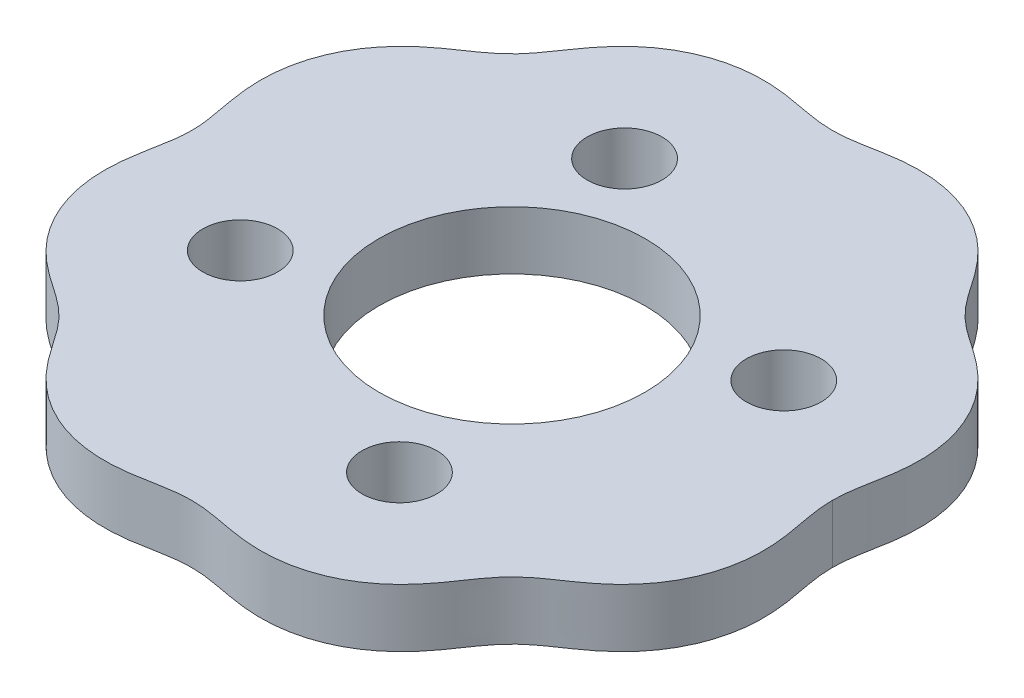
SolidWorks part; units mm, degrees
material "PET"
ref_plane "Front Plane" through (0, 0, 0) normal (0, 0, 1) x (1, 0, 0)
ref_plane "Top Plane" through (0, 0, 0) normal (0, 1, 0) x (1, 0, 0)
ref_plane "Right Plane" through (0, 0, 0) normal (1, 0, 0) x (0, 0, -1)
sketch "Sketch2" plane through (0, 0, 0) normal (0, 1, 0) x (1, 0, 0)
  line L0 (-38.5, 0) -> (38.5, 0) construction
  spline S0 degree 4 poles (38.1584, 16.3054) (38.2988, 15.991) (38.5624, 15.3567) (38.9037, 14.3799) (39.2498, 13.0497) (39.4657, 11.7929) (39.5812, 10.6379) (39.6179, 9.5697) (39.6051, 8.63) (39.5377, 7.649) (39.4431, 6.7539) (39.2854, 5.7098) (39.1515, 4.943) (38.9539, 3.8904) (38.8677, 3.4303) (38.801, 3.0463) (38.7527, 2.7604) (38.7172, 2.5417) (38.6781, 2.2874) (38.6248, 1.9059) (38.5598, 1.3568) (38.5067, 0.6636) (38.4908, -0.1341) (38.5223, -0.93) (38.5973, -1.7236) (38.714, -2.5565) (38.8656, -3.429) (39.0392, -4.3425) (39.2166, -5.3006) (39.3735, -6.2623) (39.4981, -7.2289) (39.6027, -8.4428) (39.6384, -10.0805) (39.4713, -12.1349) (38.9177, -14.5567) (37.9169, -17.0213) (36.6319, -19.1322) (35.1813, -20.8902) (33.6686, -22.3296) (32.1775, -23.5049) (30.6768, -24.5364) (29.2303, -25.5119) (27.9082, -26.5342) (26.7634, -27.6481) (25.705, -28.9579) (24.7073, -30.419) (23.6657, -31.9562) (22.4771, -33.4984) (21.0293, -35.0529) (19.267, -36.5367) (17.158, -37.8472) (14.7024, -38.8713) (11.8141, -39.559) (9.0199, -39.7053) (6.4233, -39.4363) (4.1359, -38.9993) (2.4195, -38.6732) (0.7782, -38.4852) (-0.7782, -38.4854) (-2.4196, -38.6729) (-4.1357, -38.9997) (-5.947, -39.3446) (-7.8752, -39.5874) (-9.9954, -39.6537) (-12.2881, -39.4466) (-15.349, -38.7168) (-18.2043, -37.3449) (-20.5778, -35.5386) (-22.4768, -33.4983) (-23.6659, -31.9563) (-24.7071, -30.4189) (-25.7051, -28.9579) (-26.7634, -27.6481) (-27.9082, -26.5342) (-29.2303, -25.5119) (-30.6768, -24.5364) (-32.1775, -23.5049) (-33.6686, -22.3296) (-35.1813, -20.8902) (-36.6319, -19.1322) (-37.9169, -17.0213) (-38.9177, -14.5567) (-39.4713, -12.1349) (-39.6384, -10.0805) (-39.6027, -8.4428) (-39.4981, -7.2289) (-39.3891, -6.3832) (-39.2754, -5.6612) (-39.1709, -5.0613) (-39.0832, -4.5821) (-38.9934, -4.1033) (-38.9038, -3.6244) (-38.803, -3.069) (-38.6971, -2.4358) (-38.5973, -1.7236) (-38.5223, -0.93) (-38.4908, -0.1341) (-38.5067, 0.6636) (-38.5598, 1.3568) (-38.6248, 1.9059) (-38.6781, 2.2874) (-38.7172, 2.5417) (-38.7527, 2.7604) (-38.801, 3.0463) (-38.8677, 3.4303) (-38.9539, 3.8904) (-39.1515, 4.943) (-39.2854, 5.7098) (-39.4431, 6.7539) (-39.5377, 7.649) (-39.6051, 8.63) (-39.6179, 9.5697) (-39.5812, 10.6379) (-39.4657, 11.7929) (-39.2498, 13.0497) (-38.9037, 14.3799) (-38.5624, 15.3567) (-38.2988, 15.991) (-38.1584, 16.3054) knots 0 0 0 0 0 0.00848 0.016961 0.025441 0.033921 0.039806 0.045692 0.051577 0.057462 0.063348 0.069233 0.075119 0.081004 0.083459 0.084687 0.085914 0.087142 0.08837 0.090825 0.095736 0.100646 0.105557 0.110467 0.115378 0.120289 0.126296 0.132303 0.13831 0.144317 0.150324 0.156331 0.168345 0.184674 0.201003 0.217332 0.233662 0.245354 0.257046 0.268738 0.28043 0.290252 0.300073 0.309894 0.319715 0.331705 0.343696 0.355686 0.367676 0.384005 0.400334 0.416664 0.432993 0.456925 0.468892 0.480858 0.490429 0.5 0.509571 0.519142 0.531108 0.543075 0.555041 0.567007 0.583336 0.599666 0.632324 0.644314 0.656304 0.668295 0.680285 0.690106 0.699927 0.709748 0.71957 0.731262 0.742954 0.754646 0.766338 0.782668 0.798997 0.815326 0.831655 0.843669 0.849676 0.855683 0.86169 0.864694 0.867697 0.870701 0.873704 0.876708 0.879711 0.884622 0.889533 0.894443 0.899354 0.904264 0.909175 0.91163 0.912858 0.914086 0.915313 0.916541 0.918996 0.924881 0.930767 0.936652 0.942538 0.948423 0.954308 0.960194 0.966079 0.974559 0.983039 0.99152 1 1 1 1 1 construction
  spline S1 degree 4 poles (38.5, 0) (38.5, -0.133) (38.5043, -0.4652) (38.5285, -0.9959) (38.5973, -1.7236) (38.714, -2.5565) (38.8656, -3.429) (39.0392, -4.3425) (39.2166, -5.3006) (39.3735, -6.2623) (39.4981, -7.2289) (39.6027, -8.4428) (39.6384, -10.0805) (39.4713, -12.1349) (38.9177, -14.5567) (37.9169, -17.0213) (36.6319, -19.1322) (35.1813, -20.8902) (33.6686, -22.3296) (32.1775, -23.5049) (30.6768, -24.5364) (29.2303, -25.5119) (27.9082, -26.5342) (26.7634, -27.6481) (25.705, -28.9579) (24.7073, -30.419) (23.6657, -31.9562) (22.4771, -33.4984) (21.0293, -35.0529) (19.267, -36.5367) (17.158, -37.8472) (14.7024, -38.8713) (11.8141, -39.559) (9.0199, -39.7053) (6.4233, -39.4363) (4.1359, -38.9993) (2.4195, -38.6732) (0.7782, -38.4852) (-0.7782, -38.4854) (-2.4196, -38.6729) (-4.1357, -38.9997) (-5.947, -39.3446) (-7.8752, -39.5874) (-9.9954, -39.6537) (-12.2881, -39.4466) (-15.349, -38.7168) (-18.2043, -37.3449) (-20.5778, -35.5386) (-22.4768, -33.4983) (-23.6659, -31.9563) (-24.7071, -30.4189) (-25.7051, -28.9579) (-26.7634, -27.6481) (-27.9082, -26.5342) (-29.2303, -25.5119) (-30.6768, -24.5364) (-32.1775, -23.5049) (-33.6686, -22.3296) (-35.1813, -20.8902) (-36.6319, -19.1322) (-37.9169, -17.0213) (-38.9177, -14.5567) (-39.4713, -12.1349) (-39.6384, -10.0805) (-39.6027, -8.4428) (-39.4981, -7.2289) (-39.3891, -6.3832) (-39.2754, -5.6612) (-39.1709, -5.0613) (-39.0832, -4.5821) (-38.9934, -4.1033) (-38.9038, -3.6244) (-38.803, -3.069) (-38.6971, -2.4358) (-38.5973, -1.7236) (-38.5285, -0.9959) (-38.5043, -0.4652) (-38.5, -0.133) (-38.5, 0) knots 0.102277 0.102277 0.102277 0.102277 0.102277 0.105557 0.110467 0.115378 0.120289 0.126296 0.132303 0.13831 0.144317 0.150324 0.156331 0.168345 0.184674 0.201003 0.217332 0.233662 0.245354 0.257046 0.268738 0.28043 0.290252 0.300073 0.309894 0.319715 0.331705 0.343696 0.355686 0.367676 0.384005 0.400334 0.416664 0.432993 0.456925 0.468892 0.480858 0.490429 0.5 0.509571 0.519142 0.531108 0.543075 0.555041 0.567007 0.583336 0.599666 0.632324 0.644314 0.656304 0.668295 0.680285 0.690106 0.699927 0.709748 0.71957 0.731262 0.742954 0.754646 0.766338 0.782668 0.798997 0.815326 0.831655 0.843669 0.849676 0.855683 0.86169 0.864694 0.867697 0.870701 0.873704 0.876708 0.879711 0.884622 0.889533 0.894443 0.897723 0.897723 0.897723 0.897723 0.897723
  spline S2 degree 4 poles (38.5, 0) (38.5, 0.133) (38.5043, 0.4652) (38.5285, 0.9959) (38.5973, 1.7236) (38.714, 2.5565) (38.8656, 3.429) (39.0392, 4.3425) (39.2166, 5.3006) (39.3735, 6.2623) (39.4981, 7.2289) (39.6027, 8.4428) (39.6384, 10.0805) (39.4713, 12.1349) (38.9177, 14.5567) (37.9169, 17.0213) (36.6319, 19.1322) (35.1813, 20.8902) (33.6686, 22.3296) (32.1775, 23.5049) (30.6768, 24.5364) (29.2303, 25.5119) (27.9082, 26.5342) (26.7634, 27.6481) (25.705, 28.9579) (24.7073, 30.419) (23.6657, 31.9562) (22.4771, 33.4984) (21.0293, 35.0529) (19.267, 36.5367) (17.158, 37.8472) (14.7024, 38.8713) (11.8141, 39.559) (9.0199, 39.7053) (6.4233, 39.4363) (4.1359, 38.9993) (2.4195, 38.6732) (0.7782, 38.4852) (-0.7782, 38.4854) (-2.4196, 38.6729) (-4.1357, 38.9997) (-5.947, 39.3446) (-7.8752, 39.5874) (-9.9954, 39.6537) (-12.2881, 39.4466) (-15.349, 38.7168) (-18.2043, 37.3449) (-20.5778, 35.5386) (-22.4768, 33.4983) (-23.6659, 31.9563) (-24.7071, 30.4189) (-25.7051, 28.9579) (-26.7634, 27.6481) (-27.9082, 26.5342) (-29.2303, 25.5119) (-30.6768, 24.5364) (-32.1775, 23.5049) (-33.6686, 22.3296) (-35.1813, 20.8902) (-36.6319, 19.1322) (-37.9169, 17.0213) (-38.9177, 14.5567) (-39.4713, 12.1349) (-39.6384, 10.0805) (-39.6027, 8.4428) (-39.4981, 7.2289) (-39.3891, 6.3832) (-39.2754, 5.6612) (-39.1709, 5.0613) (-39.0832, 4.5821) (-38.9934, 4.1033) (-38.9038, 3.6244) (-38.803, 3.069) (-38.6971, 2.4358) (-38.5973, 1.7236) (-38.5285, 0.9959) (-38.5043, 0.4652) (-38.5, 0.133) (-38.5, 0) knots 0.102277 0.102277 0.102277 0.102277 0.102277 0.105557 0.110467 0.115378 0.120289 0.126296 0.132303 0.13831 0.144317 0.150324 0.156331 0.168345 0.184674 0.201003 0.217332 0.233662 0.245354 0.257046 0.268738 0.28043 0.290252 0.300073 0.309894 0.319715 0.331705 0.343696 0.355686 0.367676 0.384005 0.400334 0.416664 0.432993 0.456925 0.468892 0.480858 0.490429 0.5 0.509571 0.519142 0.531108 0.543075 0.555041 0.567007 0.583336 0.599666 0.632324 0.644314 0.656304 0.668295 0.680285 0.690106 0.699927 0.709748 0.71957 0.731262 0.742954 0.754646 0.766338 0.782668 0.798997 0.815326 0.831655 0.843669 0.849676 0.855683 0.86169 0.864694 0.867697 0.870701 0.873704 0.876708 0.879711 0.884622 0.889533 0.894443 0.897723 0.897723 0.897723 0.897723 0.897723
extrude "Boss-Extrude1" add sketch "Sketch2" along normal blind 7 contours S1 S2
sketch "Sketch3" plane through (0, 7, 0) normal (0, 1, 0) x (1, 0, 0)
  line L0 (0, 0) -> (38.341, 15.8813) construction
  circle A0 centre (23.097, 9.5671) radius 4.5
  circle A1 centre (9.5671, -23.097) radius 4.5
  circle A2 centre (-23.097, -9.5671) radius 4.5
  circle A3 centre (-9.5671, 23.097) radius 4.5
  circle A4 centre (0, 0) radius 16
  spline S0 degree 4 poles (38.5, 0) (38.5, 0.133) (38.5043, 0.4652) (38.5285, 0.9959) (38.5973, 1.7236) (38.714, 2.5565) (38.8656, 3.429) (39.0392, 4.3425) (39.2166, 5.3006) (39.3735, 6.2623) (39.4981, 7.2289) (39.6027, 8.4428) (39.6384, 10.0805) (39.4713, 12.1349) (38.9177, 14.5567) (37.9169, 17.0213) (36.6319, 19.1322) (35.1813, 20.8902) (33.6686, 22.3296) (32.1775, 23.5049) (30.6768, 24.5364) (29.2303, 25.5119) (27.9082, 26.5342) (26.7634, 27.6481) (25.705, 28.9579) (24.7073, 30.419) (23.6657, 31.9562) (22.4771, 33.4984) (21.0293, 35.0529) (19.267, 36.5367) (17.158, 37.8472) (14.7024, 38.8713) (11.8141, 39.559) (9.0199, 39.7053) (6.4233, 39.4363) (4.1359, 38.9993) (2.4195, 38.6732) (0.7782, 38.4852) (-0.7782, 38.4854) (-2.4196, 38.6729) (-4.1357, 38.9997) (-5.947, 39.3446) (-7.8752, 39.5874) (-9.9954, 39.6537) (-12.2881, 39.4466) (-15.349, 38.7168) (-18.2043, 37.3449) (-20.5778, 35.5386) (-22.4768, 33.4983) (-23.6659, 31.9563) (-24.7071, 30.4189) (-25.7051, 28.9579) (-26.7634, 27.6481) (-27.9082, 26.5342) (-29.2303, 25.5119) (-30.6768, 24.5364) (-32.1775, 23.5049) (-33.6686, 22.3296) (-35.1813, 20.8902) (-36.6319, 19.1322) (-37.9169, 17.0213) (-38.9177, 14.5567) (-39.4713, 12.1349) (-39.6384, 10.0805) (-39.6027, 8.4428) (-39.4981, 7.2289) (-39.3891, 6.3832) (-39.2754, 5.6612) (-39.1709, 5.0613) (-39.0832, 4.5821) (-38.9934, 4.1033) (-38.9038, 3.6244) (-38.803, 3.069) (-38.6971, 2.4358) (-38.5973, 1.7236) (-38.5285, 0.9959) (-38.5043, 0.4652) (-38.5, 0.133) (-38.5, 0) knots 0.102277 0.102277 0.102277 0.102277 0.102277 0.105557 0.110467 0.115378 0.120289 0.126296 0.132303 0.13831 0.144317 0.150324 0.156331 0.168345 0.184674 0.201003 0.217332 0.233662 0.245354 0.257046 0.268738 0.28043 0.290252 0.300073 0.309894 0.319715 0.331705 0.343696 0.355686 0.367676 0.384005 0.400334 0.416664 0.432993 0.456925 0.468892 0.480858 0.490429 0.5 0.509571 0.519142 0.531108 0.543075 0.555041 0.567007 0.583336 0.599666 0.632324 0.644314 0.656304 0.668295 0.680285 0.690106 0.699927 0.709748 0.71957 0.731262 0.742954 0.754646 0.766338 0.782668 0.798997 0.815326 0.831655 0.843669 0.849676 0.855683 0.86169 0.864694 0.867697 0.870701 0.873704 0.876708 0.879711 0.884622 0.889533 0.894443 0.897723 0.897723 0.897723 0.897723 0.897723 construction
  point P16 (0, 0)
  dimension "D1" = 25
  dimension "D2" = 9
  dimension "D4" = 32
  dimension "D3" = 4
extrude "Cut-Extrude1" cut sketch "Sketch3" against normal blind 7
